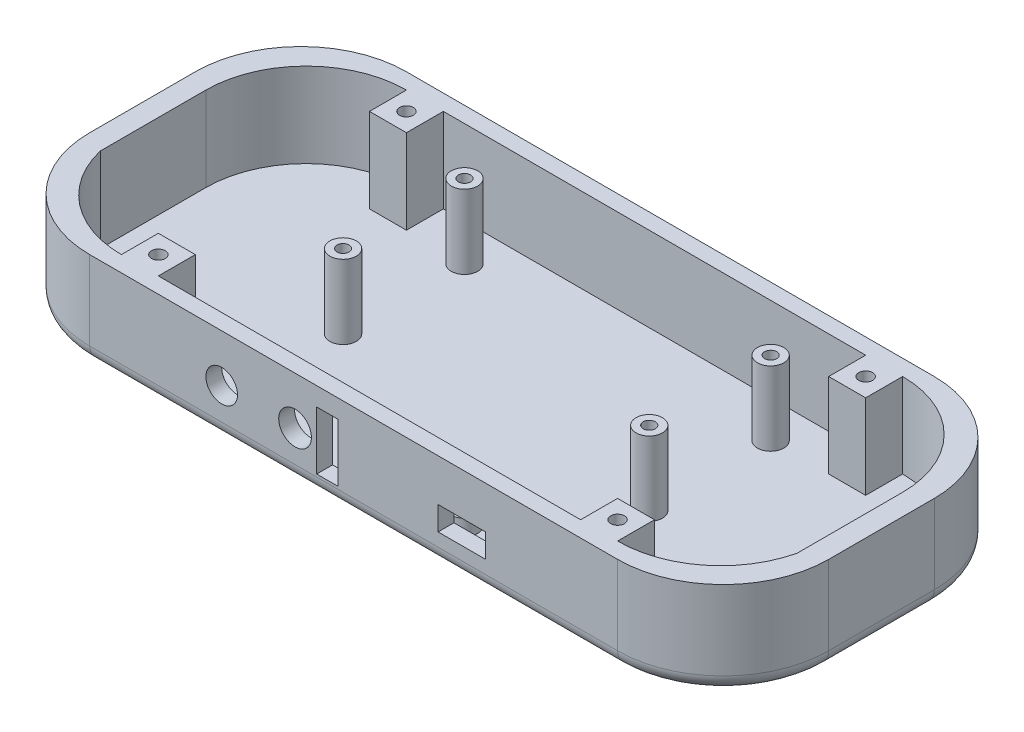
SolidWorks part; units mm, degrees
ref_plane "Front Plane" through (0, 0, 0) normal (0, 0, 1) x (1, 0, 0)
ref_plane "Top Plane" through (0, 0, 0) normal (0, 1, 0) x (1, 0, 0)
ref_plane "Right Plane" through (0, 0, 0) normal (1, 0, 0) x (0, 0, -1)
sketch "Sketch1" plane through (0, 0, 0) normal (0, 1, 0) x (1, 0, 0)
  line L0 (70, 10) -> (70, -10)
  line L1 (-50, 30) -> (50, 30)
  line L2 (-70, 10) -> (-70, -10)
  line L3 (-50, -30) -> (50, -30)
  line L5 (-50, 30) -> (50, -30) construction
  line L6 (-50, -30) -> (50, 30) construction
  arc A0 (-50, 30) -> (-70, 10) centre (-50, 10) ccw
  arc A1 (50, 30) -> (70, 10) centre (50, 10) cw
  arc A2 (-50, -30) -> (-70, -10) centre (-50, -10) cw
  arc A3 (50, -30) -> (70, -10) centre (50, -10) ccw
  point P0 (0, 0)
  dimension "D3" = 20
  dimension "D1" = 100
  dimension "D2" = 70
extrude "Boss-Extrude1" add sketch "Sketch1" along normal blind 2
sketch "Sketch2" plane through (0, 2, 0) normal (0, 1, 0) x (1, 0, 0)
  line L0 (-50, -30) -> (50, -30) construction
  line L1 (-47, 27) -> (47, 27)
  line L2 (-50, 30) -> (50, 30)
  line L3 (-47, -27) -> (47, -27)
  line L4 (70, 10) -> (70, -10)
  line L5 (-47, 27) -> (47, -27) construction
  line L6 (-47, -27) -> (47, 27) construction
  line L7 (-50, -30) -> (50, -30)
  line L8 (66, 8) -> (66, -12)
  line L9 (-50, 30) -> (50, -30) construction
  line L10 (-50, -30) -> (50, 30) construction
  line L11 (-70, 10) -> (-70, -10)
  line L13 (-66, 8) -> (-66, -12)
  arc A0 (-50, 30) -> (-70, 10) centre (-50, 10) ccw
  arc A1 (50, 30) -> (70, 10) centre (50, 10) cw
  arc A2 (-50, -30) -> (-70, -10) centre (-50, -10) cw
  arc A3 (50, -30) -> (70, -10) centre (50, -10) ccw
  arc A4 (47, 27) -> (66, 8) centre (47, 8) cw
  arc A5 (47, -27) -> (66, -12) centre (47, -7.4667) ccw
  arc A6 (-47, 27) -> (-66, 8) centre (-47, 8) ccw
  arc A7 (-47, -27) -> (-66, -12) centre (-47, -7.4667) cw
  point P0 (0, 0)
  point P8 (0, 0)
  dimension "D3" = 100
  dimension "D4" = 60
  dimension "D5" = 20
  dimension "D1" = 54
  dimension "D2" = 94
  dimension "D6" = 54
  dimension "D7" = 20
  dimension "D8" = 4
  dimension "D9" = 3
  dimension "D10" = 3
  dimension "D11" = 4
extrude "Boss-Extrude2" add sketch "Sketch2" along normal blind 16
sketch "Sketch12" plane through (0, 2, 0) normal (0, 1, 0) x (1, 0, 0)
  line L0 (-47, 27) -> (47, 27) construction
  line L1 (-47, 27) -> (-40, 27)
  line L2 (-47, 27) -> (-47, 20)
  line L3 (-47, 20) -> (-40, 20)
  line L4 (-40, 27) -> (-40, 20)
  line L5 (-47, -27) -> (-40, -27)
  line L6 (-47, -27) -> (-47, -20)
  line L7 (-47, -20) -> (-40, -20)
  line L8 (-40, -27) -> (-40, -20)
  line L9 (47, -27) -> (40, -27)
  line L10 (47, -27) -> (47, -20)
  line L11 (47, -20) -> (40, -20)
  line L12 (40, -27) -> (40, -20)
  line L13 (47, 27) -> (40, 27)
  line L14 (47, 27) -> (47, 20)
  line L15 (47, 20) -> (40, 20)
  line L16 (40, 27) -> (40, 20)
  line L17 (-47, -27) -> (47, -27) construction
  dimension "D1" = 7
  dimension "D2" = 7
  dimension "D3" = 7
  dimension "D4" = 7
  dimension "D5" = 7
  dimension "D6" = 7
  dimension "D7" = 7
  dimension "D8" = 7
  dimension "D9" = 0
  dimension "D10" = 0
  dimension "D11" = 0
  dimension "D12" = 0
  dimension "D13" = 0
  dimension "D14" = 0
extrude "Boss-Extrude5" add sketch "Sketch12" along normal blind 16
fillet "Fillet1" radius 3 8 edges at (-64.1421, 0, 24.1421) (-64.1421, 0, -24.1421) (-70, 0, 0) (0, 0, 30) (64.1421, 0, 24.1421) (70, 0, 0) (64.1421, 0, -24.1421) (0, 0, -30)
sketch "Sketch13" plane through (0, 18, 0) normal (0, 1, 0) x (1, 0, 0)
  line L0 (47, 20) -> (47, 27) construction
  line L1 (40, 20) -> (47, 20) construction
  line L2 (47, -27) -> (47, -20) construction
  line L3 (47, -20) -> (40, -20) construction
  line L4 (-40, -27) -> (-40, -20) construction
  line L5 (-40, -20) -> (-47, -20) construction
  line L6 (-47, 20) -> (-40, 20) construction
  line L7 (-47, 27) -> (-47, 20) construction
  circle A0 centre (-43.5, 23.5) radius 1.3
  circle A1 centre (-43.5, -23.5) radius 1.3
  circle A2 centre (43.5, -23.5) radius 1.3
  circle A3 centre (43.5, 23.5) radius 1.3
  dimension "D1" = 2.6
  dimension "D2" = 2.6
  dimension "D3" = 2.6
  dimension "D4" = 2.6
  dimension "D7" = 3.5
  dimension "D8" = 3.5
  dimension "D9" = 3.5
  dimension "D11" = 3.5
  dimension "D12" = 3.5
  dimension "D5" = 3.5
  dimension "D6" = 3.5
  dimension "D10" = 3.5
extrude "Cut-Extrude7" cut sketch "Sketch13" against normal through all
sketch "Sketch14" plane through (0, 2, 0) normal (0, 1, 0) x (1, 0, 0)
  line L1 (-40, 27) -> (40, 27) construction
  circle A0 centre (29, -3) radius 2.5
  circle A1 centre (29, 20) radius 2.5
  circle A2 centre (-29, 20) radius 2.5
  circle A3 centre (-29, -3) radius 2.5
  circle A4 centre (29, -3) radius 1.15
  circle A5 centre (29, 20) radius 1.15
  circle A6 centre (-29, 20) radius 1.15
  circle A7 centre (-29, -3) radius 1.15
  dimension "D1" = 5
  dimension "D2" = 5
  dimension "D3" = 5
  dimension "D4" = 5
  dimension "D6" = 29
  dimension "D7" = 29
  dimension "D8" = 29
  dimension "D9" = 58
  dimension "D10" = 58
  dimension "D11" = 7
  dimension "D12" = 23
  dimension "D13" = 2.3
  dimension "D14" = 2.3
  dimension "D15" = 2.3
  dimension "D16" = 2.3
  dimension "D5" = 29
extrude "Boss-Extrude6" add sketch "Sketch14" along normal blind 14
sketch "Sketch15" plane through (0, 2, 0) normal (0, 1, 0) x (1, 0, 0)
  line L1 (-40, -27) -> (40, -27) construction
  circle A0 centre (29, -23) radius 2.5
  circle A1 centre (14, -23) radius 2.5
  circle A2 centre (29, -23) radius 1.3
  circle A3 centre (14, -23) radius 1.3
  dimension "D1" = 5
  dimension "D2" = 5
  dimension "D4" = 15
  dimension "D7" = 2.6
  dimension "D8" = 2.6
  dimension "D5" = 4
  dimension "D6" = 4
extrude "Boss-Extrude7" add sketch "Sketch15" along normal blind 3
sketch "Sketch16" plane through (0, 0, 27) normal (0, 0, -1) x (-1, 0, 0)
  line L0 (-40, 18) -> (-40, 2) construction
  line L1 (-25, 10) -> (-16, 10)
  line L2 (-25, 10) -> (-25, 5.5)
  line L3 (-25, 5.5) -> (-16, 5.5)
  line L4 (-16, 10) -> (-16, 5.5)
  line L5 (-25, 10) -> (-16, 5.5) construction
  line L6 (-25, 5.5) -> (-16, 10) construction
  line L7 (40, 2) -> (-40, 2) construction
  point P0 (-20.5, 7.75)
  dimension "D1" = 15
  dimension "D2" = 9
  dimension "D3" = 4.5
  dimension "D4" = 3.5
extrude "Cut-Extrude8" cut sketch "Sketch16" against normal through all
sketch "Sketch17" plane through (0, 0, 0) normal (0, -1, 0) x (1, 0, 0)
  circle A0 centre (-43.5, 23.5) radius 3.25
  circle A1 centre (43.5, 23.5) radius 3.25
  circle A2 centre (43.5, -23.5) radius 3.25
  circle A3 centre (-43.5, -23.5) radius 3.25
  dimension "D1" = 6.5
  dimension "D2" = 6.5
  dimension "D3" = 6.5
  dimension "D4" = 6.5
extrude "Cut-Extrude9" cut sketch "Sketch17" against normal blind 13
sketch "Sketch19" plane through (0, 0, 27) normal (0, 0, -1) x (-1, 0, 0)
  line L0 (-16, 5.5) -> (-16, 10) construction
  line L1 (40, 2) -> (-40, 2) construction
  circle A0 centre (-1, 9) radius 2.5
  circle A1 centre (34, 9) radius 2.5
  circle A2 centre (-1, 9) radius 1.15
  circle A3 centre (34, 9) radius 1.15
  dimension "D1" = 5
  dimension "D2" = 5
  dimension "D3" = 35
  dimension "D6" = 7
  dimension "D7" = 2.3
  dimension "D8" = 2.3
  dimension "D4" = 15
  dimension "D5" = 7
extrude "Boss-Extrude8" add sketch "Sketch19" along normal blind 2.5
sketch "Sketch20" plane through (0, 0, 27) normal (0, 0, -1) x (-1, 0, 0)
  line L0 (40, 2) -> (-40, 2) construction
  line L1 (3, 14.5) -> (7, 14.5)
  line L2 (3, 14.5) -> (3, 3.5)
  line L3 (3, 3.5) -> (7, 3.5)
  line L4 (7, 14.5) -> (7, 3.5)
  line L5 (3, 14.5) -> (7, 3.5) construction
  line L6 (3, 3.5) -> (7, 14.5) construction
  circle A0 centre (-1, 9) radius 1.15 construction
  circle A1 centre (11.1, 9) radius 3.1
  circle A2 centre (25, 9) radius 3
  circle A3 centre (34, 9) radius 1.15 construction
  point P0 (5, 9)
  dimension "D2" = 0
  dimension "D4" = 4
  dimension "D5" = 6.2
  dimension "D6" = 7
  dimension "D7" = 12.1
  dimension "D8" = 7
  dimension "D9" = 6
  dimension "D10" = 9
  dimension "D1" = 11
  dimension "D3" = 4
extrude "Cut-Extrude10" cut sketch "Sketch20" against normal blind 5
sketch "Sketch21" plane through (0, 0, 24.5) normal (0, 0, -1) x (-1, 0, 0)
  circle A0 centre (-1, 9) radius 1.15
extrude "Cut-Extrude11" cut sketch "Sketch21" against normal blind 3.5
sketch "Sketch22" plane through (0, 0, 24.5) normal (0, 0, -1) x (-1, 0, 0)
  circle A0 centre (34, 9) radius 1.15
extrude "Cut-Extrude12" cut sketch "Sketch22" against normal blind 3.5
